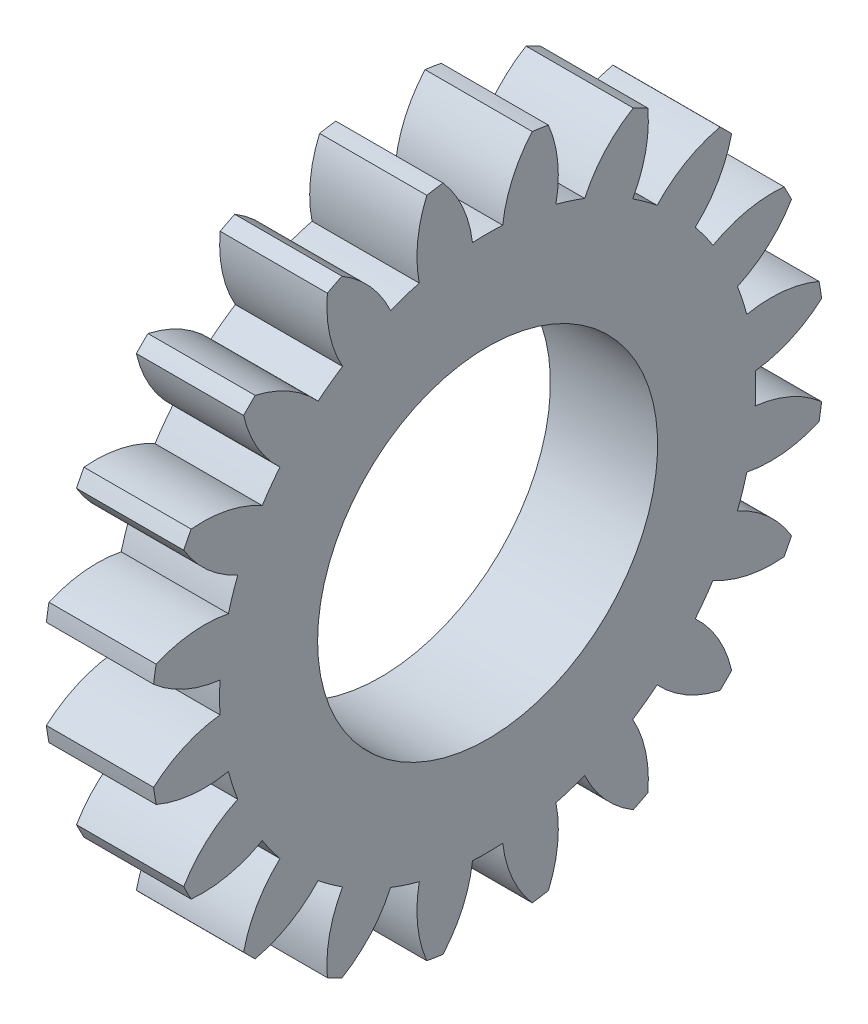
SolidWorks part; units mm, degrees
ref_plane "Plane1" through (0, 0, 0) normal (0, 0, 1) x (1, 0, 0)
ref_plane "Plane2" through (0, 0, 0) normal (0, 1, 0) x (1, 0, 0)
ref_plane "Plane3" through (0, 0, 0) normal (1, 0, 0) x (0, 0, -1)
other "Configuration Table"
sketch "HoldingSke" plane through (0, 0, 0) normal (0, 1, 0) x (1, 0, 0)
  line L0 (0, 0) -> (0.4698, -0.171)
  line L1 (-15, 0) -> (100, 0) construction
  line L2 (0, 0) -> (-2.1039, 2.3779)
  line L3 (0, 0) -> (-11.863, 4.5341)
  line L4 (0, 0) -> (8.1152, 2.9537)
  line L5 (0, 0) -> (-46.8476, -17.4728)
  line L6 (0, 0) -> (-12.4344, -8.3896)
  line L7 (-2.1039, 2.3779) -> (8.6586, 51.2059)
  line L8 (-76.2, 54.61) -> (-76.1, 54.61)
  line L9 (-71.009, 38.7566) -> (-53.1078, 45.2721)
  line L10 (-76.2, 71.12) -> (104.1128, 71.12)
  line L11 (0, 0) -> (-15, 0)
  line L12 (-76.2, 101.6) -> (-76.133, 101.6)
  line L13 (24.9733, 27.94) -> (52.9518, 28.4284)
  line L14 (24.9733, 27.94) -> (24.9743, 27.94)
  line L15 (24.9733, 27.94) -> (100.4006, 29.5858)
  line L16 (-63.627, -2) -> (-12.827, -2)
  circle A0 centre (0, 0) radius 0.5
  circle A1 centre (0, 0) radius 17.499
  circle A2 centre (0, 0) radius 37.5
  circle A3 centre (0, 0) radius 0.5
  dimension "MHD" = 34.998
  dimension "Hub_dia" = 75
  dimension "Bore" = 1
  dimension "MBD" = 1
  dimension "Num_teeth" = 20
  dimension "Pitch" = 0.5
  dimension "Overall_len" = 50
  dimension "Show_teeth" = 20
  dimension "Thickness" = 15
  dimension "OAL" = 50.0001
  dimension "T_dim" = 0.1
  dimension "Ap" = 20
  dimension "H" = 19.05
  dimension "Pitch_radius" = 180.3128
  dimension "Width" = 15
  dimension "Backlash" = 0.067
  dimension "Addendum_fac" = 1
  dimension "Dedendum_fac" = 1.25
  dimension "Clearance_fac" = 0.25
  dimension "Dedendum_add" = 0.001
  dimension "Module" = 2
sketch "BasProSke" plane through (0, 0, 0) normal (0, 1, 0) x (1, 0, 0)
  line L0 (-10, 0) -> (60, 0) construction
  line L1 (0, 0) -> (0, 22)
  line L2 (0, 0) -> (15, 0)
  line L3 (15, 0) -> (15, 22)
  line L4 (15, 22) -> (0, 22)
  dimension "Thickness" = 15
  dimension "Diameter" = 44
revolve "Base-Revolve" add sketch "BasProSke" angle 360 about L0
sketch "TooCutSke" plane through (0, 0, 0) normal (1, 0, 0) x (0, 0, -1)
  line L1 (0, 0) -> (0, 107) construction
  line L2 (0, 0) -> (-1.6864, 19.9288) construction
  line L3 (0, 0) -> (-6.2409, 39.4033) construction
  line L4 (-1.6864, 19.9288) -> (-3.1204, 19.7016) construction
  arc A0 (0.9862, 17.4712) -> (-0.9862, 17.4712) centre (0, 0) ccw
  arc A1 (2.9329, 21.8293) -> (-2.9329, 21.8293) centre (0, 0) ccw
  circle A2 centre (0, 0) radius 20 construction
  circle A3 centre (0, 0) radius 18.7939 construction
  arc A4 (-0.9862, 17.4712) -> (-2.9329, 21.8293) centre (-8.9313, 16.536) ccw
  arc A5 (2.9329, 21.8293) -> (0.9862, 17.4712) centre (8.9313, 16.536) ccw
  dimension "Root_dia" = 34.998
  dimension "Overcut_dia" = 44.0508
  dimension "Pitch_dia" = 40
  dimension "Base_dia" = 37.5877
  dimension "Flank_rad" = 8
  dimension "Half_ang" = 9
  dimension "Half_CT" = 1.4519
extrude "ToothCut" cut sketch "TooCutSke" along normal through all
fillet "Breaks" [suppressed] radius 0.04
fillet "RootFillets" [suppressed] radius 0.501
pattern_circular "TeethCuts" count 20 every 18 about axis through (-10, 0, 0) along (1, 0, 0) of "ToothCut", "RootFillets", "Breaks"
sketch "HubNeaOneSke" plane through (0, 0, 0) normal (-1, 0, 0) x (0, 0, 1)
  circle A0 centre (0, 0) radius 17.499
  dimension "Diameter" = 34.998
extrude "HubNearOne" [suppressed] add sketch "HubNeaOneSke" along normal blind 35.0001
sketch "HubNeaBotSke" plane through (0, 0, 0) normal (-1, 0, 0) x (0, 0, 1)
  circle A0 centre (0, 0) radius 17.499
  dimension "Diameter" = 34.998
extrude "HubNearBoth" [suppressed] add sketch "HubNeaBotSke" along normal blind 17.5
ref_plane "FarPln" through (15, 0, 0) normal (1, 0, 0) x (0, 0, -1)
sketch "HubFarSke" plane through (15, 0, 0) normal (1, 0, 0) x (0, 0, -1)
  circle A0 centre (0, 0) radius 17.499
  dimension "Diameter" = 34.998
extrude "HubFar" [suppressed] add sketch "HubFarSke" along normal blind 17.5
sketch "BorSke" plane through (0, 0, 0) normal (1, 0, 0) x (0, 0, -1)
  circle A0 centre (0, 0) radius 0.5
  dimension "Diameter" = 1
extrude "Bore" cut sketch "BorSke" along normal mid plane 100.0001
sketch "KeySke" plane through (0, 0, 0) normal (1, 0, 0) x (0, 0, -1)
  line L0 (-0.05, 0) -> (-0.05, 0.6)
  line L1 (-0.05, 0.6) -> (0.05, 0.6)
  line L2 (0.05, 0.6) -> (0.05, 0)
  line L3 (0, 0) -> (0, 34) construction
  line L4 (-0.05, 0) -> (0.05, 0)
  dimension "Offset" = 0.6
  dimension "Width" = 0.1
extrude "Keyway" [suppressed] cut sketch "KeySke" along normal mid plane 100.0001
pattern_circular "Keyway2" [suppressed] count 2 every 90 about axis through (-10, 0, 0) along (1, 0, 0)
sketch "Sketch1" plane through (0, 0, 0) normal (-1, 0, 0) x (0, 0, 1)
  circle A0 centre (0, 0) radius 11.1
extrude "Cut-Extrude1" cut sketch "Sketch1" against normal blind 16
sketch "Sketch2" plane through (0, 0, 0) normal (-1, 0, 0) x (0, 0, 1)
  arc A80 (17.4712, 0.9862) -> (21.8063, 2.9127) centre (16.536, 8.9313) ccw
  arc A81 (21.8063, 2.9127) -> (21.6391, 3.9684) centre (0, 0) ccw
  arc A82 (21.6391, 3.9684) -> (16.9208, 4.461) centre (18.4866, -3.3843) ccw
  arc A83 (16.9208, 4.461) -> (16.3113, 6.3368) centre (0, 0) ccw
  arc A84 (16.3113, 6.3368) -> (19.839, 9.5087) centre (12.9668, 13.6041) ccw
  arc A85 (19.839, 9.5087) -> (19.3537, 10.461) centre (0, 0) ccw
  arc A86 (19.3537, 10.461) -> (14.7141, 9.4715) centre (18.6276, 2.494) ccw
  arc A87 (14.7141, 9.4715) -> (13.5548, 11.0671) centre (0, 0) ccw
  arc A88 (13.5548, 11.0671) -> (15.9297, 15.1739) centre (8.1282, 16.9452) ccw
  arc A89 (15.9297, 15.1739) -> (15.1739, 15.9297) centre (0, 0) ccw
  arc A90 (15.1739, 15.9297) -> (11.0671, 13.5548) centre (16.9452, 8.1282) ccw
  arc A91 (11.0671, 13.5548) -> (9.4715, 14.7141) centre (0, 0) ccw
  arc A92 (9.4715, 14.7141) -> (10.461, 19.3537) centre (2.494, 18.6276) ccw
  arc A93 (10.461, 19.3537) -> (9.5087, 19.839) centre (0, 0) ccw
  arc A94 (9.5087, 19.839) -> (6.3368, 16.3113) centre (13.6041, 12.9668) ccw
  arc A95 (6.3368, 16.3113) -> (4.461, 16.9208) centre (0, 0) ccw
  arc A96 (4.461, 16.9208) -> (3.9684, 21.6391) centre (-3.3843, 18.4866) ccw
  arc A97 (3.9684, 21.6391) -> (2.9127, 21.8063) centre (0, 0) ccw
  arc A98 (2.9127, 21.8063) -> (0.9862, 17.4712) centre (8.9313, 16.536) ccw
  arc A99 (0.9862, 17.4712) -> (-0.9862, 17.4712) centre (0, 0) ccw
  arc A100 (-0.9862, 17.4712) -> (-2.9127, 21.8063) centre (-8.9313, 16.536) ccw
  arc A101 (-2.9127, 21.8063) -> (-3.9684, 21.6391) centre (0, 0) ccw
  arc A102 (-3.9684, 21.6391) -> (-4.461, 16.9208) centre (3.3843, 18.4866) ccw
  arc A103 (-4.461, 16.9208) -> (-6.3368, 16.3113) centre (0, 0) ccw
  arc A104 (-6.3368, 16.3113) -> (-9.5087, 19.839) centre (-13.6041, 12.9668) ccw
  arc A105 (-9.5087, 19.839) -> (-10.461, 19.3537) centre (0, 0) ccw
  arc A106 (-10.461, 19.3537) -> (-9.4715, 14.7141) centre (-2.494, 18.6276) ccw
  arc A107 (-9.4715, 14.7141) -> (-11.0671, 13.5548) centre (0, 0) ccw
  arc A108 (-11.0671, 13.5548) -> (-15.1739, 15.9297) centre (-16.9452, 8.1282) ccw
  arc A109 (-15.1739, 15.9297) -> (-15.9297, 15.1739) centre (0, 0) ccw
  arc A110 (-15.9297, 15.1739) -> (-13.5548, 11.0671) centre (-8.1282, 16.9452) ccw
  arc A111 (-13.5548, 11.0671) -> (-14.7141, 9.4715) centre (0, 0) ccw
  arc A112 (-14.7141, 9.4715) -> (-19.3537, 10.461) centre (-18.6276, 2.494) ccw
  arc A113 (-19.3537, 10.461) -> (-19.839, 9.5087) centre (0, 0) ccw
  arc A114 (-19.839, 9.5087) -> (-16.3113, 6.3368) centre (-12.9668, 13.6041) ccw
  arc A115 (-16.3113, 6.3368) -> (-16.9208, 4.461) centre (0, 0) ccw
  arc A116 (-16.9208, 4.461) -> (-21.6391, 3.9684) centre (-18.4866, -3.3843) ccw
  arc A117 (-21.6391, 3.9684) -> (-21.8063, 2.9127) centre (0, 0) ccw
  arc A118 (-21.8063, 2.9127) -> (-17.4712, 0.9862) centre (-16.536, 8.9313) ccw
  arc A119 (-17.4712, 0.9862) -> (-17.4712, -0.9862) centre (0, 0) ccw
  arc A120 (-17.4712, -0.9862) -> (-21.8063, -2.9127) centre (-16.536, -8.9313) ccw
  arc A121 (-21.8063, -2.9127) -> (-21.6391, -3.9684) centre (0, 0) ccw
  arc A122 (-21.6391, -3.9684) -> (-16.9208, -4.461) centre (-18.4866, 3.3843) ccw
  arc A123 (-16.9208, -4.461) -> (-16.3113, -6.3368) centre (0, 0) ccw
  arc A124 (-16.3113, -6.3368) -> (-19.839, -9.5087) centre (-12.9668, -13.6041) ccw
  arc A125 (-19.839, -9.5087) -> (-19.3537, -10.461) centre (0, 0) ccw
  arc A126 (-19.3537, -10.461) -> (-14.7141, -9.4715) centre (-18.6276, -2.494) ccw
  arc A127 (-14.7141, -9.4715) -> (-13.5548, -11.0671) centre (0, 0) ccw
  arc A128 (-13.5548, -11.0671) -> (-15.9297, -15.1739) centre (-8.1282, -16.9452) ccw
  arc A129 (-15.9297, -15.1739) -> (-15.1739, -15.9297) centre (0, 0) ccw
  arc A130 (-15.1739, -15.9297) -> (-11.0671, -13.5548) centre (-16.9452, -8.1282) ccw
  arc A131 (-11.0671, -13.5548) -> (-9.4715, -14.7141) centre (0, 0) ccw
  arc A132 (-9.4715, -14.7141) -> (-10.461, -19.3537) centre (-2.494, -18.6276) ccw
  arc A133 (-10.461, -19.3537) -> (-9.5087, -19.839) centre (0, 0) ccw
  arc A134 (-9.5087, -19.839) -> (-6.3368, -16.3113) centre (-13.6041, -12.9668) ccw
  arc A135 (-6.3368, -16.3113) -> (-4.461, -16.9208) centre (0, 0) ccw
  arc A136 (-4.461, -16.9208) -> (-3.9684, -21.6391) centre (3.3843, -18.4866) ccw
  arc A137 (-3.9684, -21.6391) -> (-2.9127, -21.8063) centre (0, 0) ccw
  arc A138 (-2.9127, -21.8063) -> (-0.9862, -17.4712) centre (-8.9313, -16.536) ccw
  arc A139 (-0.9862, -17.4712) -> (0.9862, -17.4712) centre (0, 0) ccw
  arc A140 (0.9862, -17.4712) -> (2.9127, -21.8063) centre (8.9313, -16.536) ccw
  arc A141 (2.9127, -21.8063) -> (3.9684, -21.6391) centre (0, 0) ccw
  arc A142 (3.9684, -21.6391) -> (4.461, -16.9208) centre (-3.3843, -18.4866) ccw
  arc A143 (4.461, -16.9208) -> (6.3368, -16.3113) centre (0, 0) ccw
  arc A144 (6.3368, -16.3113) -> (9.5087, -19.839) centre (13.6041, -12.9668) ccw
  arc A145 (9.5087, -19.839) -> (10.461, -19.3537) centre (0, 0) ccw
  arc A146 (10.461, -19.3537) -> (9.4715, -14.7141) centre (2.494, -18.6276) ccw
  arc A147 (9.4715, -14.7141) -> (11.0671, -13.5548) centre (0, 0) ccw
  arc A148 (11.0671, -13.5548) -> (15.1739, -15.9297) centre (16.9452, -8.1282) ccw
  arc A149 (15.1739, -15.9297) -> (15.9297, -15.1739) centre (0, 0) ccw
  arc A150 (15.9297, -15.1739) -> (13.5548, -11.0671) centre (8.1282, -16.9452) ccw
  arc A151 (13.5548, -11.0671) -> (14.7141, -9.4715) centre (0, 0) ccw
  arc A152 (14.7141, -9.4715) -> (19.3537, -10.461) centre (18.6276, -2.494) ccw
  arc A153 (19.3537, -10.461) -> (19.839, -9.5087) centre (0, 0) ccw
  arc A154 (19.839, -9.5087) -> (16.3113, -6.3368) centre (12.9668, -13.6041) ccw
  arc A155 (16.3113, -6.3368) -> (16.9208, -4.461) centre (0, 0) ccw
  arc A156 (16.9208, -4.461) -> (21.6391, -3.9684) centre (18.4866, 3.3843) ccw
  arc A157 (21.6391, -3.9684) -> (21.8063, -2.9127) centre (0, 0) ccw
  arc A158 (21.8063, -2.9127) -> (17.4712, -0.9862) centre (16.536, -8.9313) ccw
  arc A159 (17.4712, -0.9862) -> (17.4712, 0.9862) centre (0, 0) ccw
  arc A160 (17.4712, 0.9862) -> (21.8063, 2.9127) centre (16.536, 8.9313) ccw
  arc A161 (21.8063, 2.9127) -> (21.6391, 3.9684) centre (0, 0) ccw
  arc A162 (21.6391, 3.9684) -> (16.9208, 4.461) centre (18.4866, -3.3843) ccw
  arc A163 (16.9208, 4.461) -> (16.3113, 6.3368) centre (0, 0) ccw
  arc A164 (16.3113, 6.3368) -> (19.839, 9.5087) centre (12.9668, 13.6041) ccw
  arc A165 (19.839, 9.5087) -> (19.3537, 10.461) centre (0, 0) ccw
  arc A166 (19.3537, 10.461) -> (14.7141, 9.4715) centre (18.6276, 2.494) ccw
  arc A167 (14.7141, 9.4715) -> (13.5548, 11.0671) centre (0, 0) ccw
  arc A168 (13.5548, 11.0671) -> (15.9297, 15.1739) centre (8.1282, 16.9452) ccw
  arc A169 (15.9297, 15.1739) -> (15.1739, 15.9297) centre (0, 0) ccw
  arc A170 (15.1739, 15.9297) -> (11.0671, 13.5548) centre (16.9452, 8.1282) ccw
  arc A171 (11.0671, 13.5548) -> (9.4715, 14.7141) centre (0, 0) ccw
  arc A172 (9.4715, 14.7141) -> (10.461, 19.3537) centre (2.494, 18.6276) ccw
  arc A173 (10.461, 19.3537) -> (9.5087, 19.839) centre (0, 0) ccw
  arc A174 (9.5087, 19.839) -> (6.3368, 16.3113) centre (13.6041, 12.9668) ccw
  arc A175 (6.3368, 16.3113) -> (4.461, 16.9208) centre (0, 0) ccw
  arc A176 (4.461, 16.9208) -> (3.9684, 21.6391) centre (-3.3843, 18.4866) ccw
  arc A177 (3.9684, 21.6391) -> (2.9127, 21.8063) centre (0, 0) ccw
  arc A178 (2.9127, 21.8063) -> (0.9862, 17.4712) centre (8.9313, 16.536) ccw
  arc A179 (0.9862, 17.4712) -> (-0.9862, 17.4712) centre (0, 0) ccw
  arc A180 (-0.9862, 17.4712) -> (-2.9127, 21.8063) centre (-8.9313, 16.536) ccw
  arc A181 (-2.9127, 21.8063) -> (-3.9684, 21.6391) centre (0, 0) ccw
  arc A182 (-3.9684, 21.6391) -> (-4.461, 16.9208) centre (3.3843, 18.4866) ccw
  arc A183 (-4.461, 16.9208) -> (-6.3368, 16.3113) centre (0, 0) ccw
  arc A184 (-6.3368, 16.3113) -> (-9.5087, 19.839) centre (-13.6041, 12.9668) ccw
  arc A185 (-9.5087, 19.839) -> (-10.461, 19.3537) centre (0, 0) ccw
  arc A186 (-10.461, 19.3537) -> (-9.4715, 14.7141) centre (-2.494, 18.6276) ccw
  arc A187 (-9.4715, 14.7141) -> (-11.0671, 13.5548) centre (0, 0) ccw
  arc A188 (-11.0671, 13.5548) -> (-15.1739, 15.9297) centre (-16.9452, 8.1282) ccw
  arc A189 (-15.1739, 15.9297) -> (-15.9297, 15.1739) centre (0, 0) ccw
  arc A190 (-15.9297, 15.1739) -> (-13.5548, 11.0671) centre (-8.1282, 16.9452) ccw
  arc A191 (-13.5548, 11.0671) -> (-14.7141, 9.4715) centre (0, 0) ccw
  arc A192 (-14.7141, 9.4715) -> (-19.3537, 10.461) centre (-18.6276, 2.494) ccw
  arc A193 (-19.3537, 10.461) -> (-19.839, 9.5087) centre (0, 0) ccw
  arc A194 (-19.839, 9.5087) -> (-16.3113, 6.3368) centre (-12.9668, 13.6041) ccw
  arc A195 (-16.3113, 6.3368) -> (-16.9208, 4.461) centre (0, 0) ccw
  arc A196 (-16.9208, 4.461) -> (-21.6391, 3.9684) centre (-18.4866, -3.3843) ccw
  arc A197 (-21.6391, 3.9684) -> (-21.8063, 2.9127) centre (0, 0) ccw
  arc A198 (-21.8063, 2.9127) -> (-17.4712, 0.9862) centre (-16.536, 8.9313) ccw
  arc A199 (-17.4712, 0.9862) -> (-17.4712, -0.9862) centre (0, 0) ccw
  arc A200 (-17.4712, -0.9862) -> (-21.8063, -2.9127) centre (-16.536, -8.9313) ccw
  arc A201 (-21.8063, -2.9127) -> (-21.6391, -3.9684) centre (0, 0) ccw
  arc A202 (-21.6391, -3.9684) -> (-16.9208, -4.461) centre (-18.4866, 3.3843) ccw
  arc A203 (-16.9208, -4.461) -> (-16.3113, -6.3368) centre (0, 0) ccw
  arc A204 (-16.3113, -6.3368) -> (-19.839, -9.5087) centre (-12.9668, -13.6041) ccw
  arc A205 (-19.839, -9.5087) -> (-19.3537, -10.461) centre (0, 0) ccw
  arc A206 (-19.3537, -10.461) -> (-14.7141, -9.4715) centre (-18.6276, -2.494) ccw
  arc A207 (-14.7141, -9.4715) -> (-13.5548, -11.0671) centre (0, 0) ccw
  arc A208 (-13.5548, -11.0671) -> (-15.9297, -15.1739) centre (-8.1282, -16.9452) ccw
  arc A209 (-15.9297, -15.1739) -> (-15.1739, -15.9297) centre (0, 0) ccw
  arc A210 (-15.1739, -15.9297) -> (-11.0671, -13.5548) centre (-16.9452, -8.1282) ccw
  arc A211 (-11.0671, -13.5548) -> (-9.4715, -14.7141) centre (0, 0) ccw
  arc A212 (-9.4715, -14.7141) -> (-10.461, -19.3537) centre (-2.494, -18.6276) ccw
  arc A213 (-10.461, -19.3537) -> (-9.5087, -19.839) centre (0, 0) ccw
  arc A214 (-9.5087, -19.839) -> (-6.3368, -16.3113) centre (-13.6041, -12.9668) ccw
  arc A215 (-6.3368, -16.3113) -> (-4.461, -16.9208) centre (0, 0) ccw
  arc A216 (-4.461, -16.9208) -> (-3.9684, -21.6391) centre (3.3843, -18.4866) ccw
  arc A217 (-3.9684, -21.6391) -> (-2.9127, -21.8063) centre (0, 0) ccw
  arc A218 (-2.9127, -21.8063) -> (-0.9862, -17.4712) centre (-8.9313, -16.536) ccw
  arc A219 (-0.9862, -17.4712) -> (0.9862, -17.4712) centre (0, 0) ccw
  arc A220 (0.9862, -17.4712) -> (2.9127, -21.8063) centre (8.9313, -16.536) ccw
  arc A221 (2.9127, -21.8063) -> (3.9684, -21.6391) centre (0, 0) ccw
  arc A222 (3.9684, -21.6391) -> (4.461, -16.9208) centre (-3.3843, -18.4866) ccw
  arc A223 (4.461, -16.9208) -> (6.3368, -16.3113) centre (0, 0) ccw
  arc A224 (6.3368, -16.3113) -> (9.5087, -19.839) centre (13.6041, -12.9668) ccw
  arc A225 (9.5087, -19.839) -> (10.461, -19.3537) centre (0, 0) ccw
  arc A226 (10.461, -19.3537) -> (9.4715, -14.7141) centre (2.494, -18.6276) ccw
  arc A227 (9.4715, -14.7141) -> (11.0671, -13.5548) centre (0, 0) ccw
  arc A228 (11.0671, -13.5548) -> (15.1739, -15.9297) centre (16.9452, -8.1282) ccw
  arc A229 (15.1739, -15.9297) -> (15.9297, -15.1739) centre (0, 0) ccw
  arc A230 (15.9297, -15.1739) -> (13.5548, -11.0671) centre (8.1282, -16.9452) ccw
  arc A231 (13.5548, -11.0671) -> (14.7141, -9.4715) centre (0, 0) ccw
  arc A232 (14.7141, -9.4715) -> (19.3537, -10.461) centre (18.6276, -2.494) ccw
  arc A233 (19.3537, -10.461) -> (19.839, -9.5087) centre (0, 0) ccw
  arc A234 (19.839, -9.5087) -> (16.3113, -6.3368) centre (12.9668, -13.6041) ccw
  arc A235 (16.3113, -6.3368) -> (16.9208, -4.461) centre (0, 0) ccw
  arc A236 (16.9208, -4.461) -> (21.6391, -3.9684) centre (18.4866, 3.3843) ccw
  arc A237 (21.6391, -3.9684) -> (21.8063, -2.9127) centre (0, 0) ccw
  arc A238 (21.8063, -2.9127) -> (17.4712, -0.9862) centre (16.536, -8.9313) ccw
  arc A239 (17.4712, -0.9862) -> (17.4712, 0.9862) centre (0, 0) ccw
  dimension "D1" = 0
extrude "Cut-Extrude2" cut sketch "Sketch2" against normal blind 8
equation "' \"Module@HoldingSke\" = 6.35"
equation "' \"Num_teeth@HoldingSke\" = 12"
equation "' \"Ap@HoldingSke\" =  20"
equation "' \"Ap@HoldingSke\" = 20"
equation "' \"Width@HoldingSke\" = 0.5 * 25.4"
equation "' \"Hub_dia@HoldingSke\"= 1 * 25.4"
equation "' \"Hub_dia@HoldingSke\" = 1 * 25.4"
equation "' \"Overall_len@HoldingSke\" = 1.0 * 25.4"
equation "' \"Bore@HoldingSke\" = 0.75 * 25.4"
equation "' \"T_dim@HoldingSke\" = 0.1 * 25.4"
equation "' \"Width@KeySke\" = 0.25 * 25.4"
equation "' \"Show_teeth@HoldingSke\" = 13"
equation "' \"Backlash@HoldingSke\" = 0.009 * 25.4"
equation "' \"Addendum_fac@HoldingSke\" = 1.0"
equation "' \"Dedendum_fac@HoldingSke\" = 1.25"
equation "' \"Dedendum_add@HoldingSke\" = 0.00005 * 25.4"
equation "' \"Clearance_fac@HoldingSke\" = 0.25"
equation "\"Pitch@HoldingSke\" = 1 / \"Module@HoldingSke\""
equation "\"Overcut_dia@TooCutSke\" = (\"Num_teeth@HoldingSke\" + 2 * \"Addendum_fac@HoldingSke\") / \"Pitch@HoldingSke\" + 0.002 * 25.4"
equation "\"Pitch_dia@TooCutSke\" = \"Num_teeth@HoldingSke\" / \"Pitch@HoldingSke\""
equation "\"Base_dia@TooCutSke\" = \"Num_teeth@HoldingSke\" / \"Pitch@HoldingSke\" * cos((\"Ap@HoldingSke\"  * 3.14159265 / 180))"
equation "\"Root_dia@TooCutSke\" = (\"Num_teeth@HoldingSke\" + 2) / \"Pitch@HoldingSke\" - 2 * (\"Addendum_fac@HoldingSke\" + \"Dedendum_fac@HoldingSke\") / \"Pitch@HoldingSke\" - \"Dedendum_add@HoldingSke\" * 2"
equation "\"Half_ang@TooCutSke\" = 180 / \"Num_teeth@HoldingSke\""
equation "\"Half_CT@TooCutSke\" = \"Num_teeth@HoldingSke\" / \"Pitch@HoldingSke\" * sin((3.14159265 / 2 / \"Num_teeth@HoldingSke\")) / 2 - 7 * \"Backlash@HoldingSke\" / 4"
equation "\"Flank_rad@TooCutSke\" = \"Num_teeth@HoldingSke\" / \"Pitch@HoldingSke\" / 5"
equation "\"Radius@RootFillets\" = \"Clearance_fac@HoldingSke\" / \"Pitch@HoldingSke\" + \"Dedendum_add@HoldingSke\""
equation "\"Break_rad@Breaks\" = 0.02 / \"Pitch@HoldingSke\""
equation "\"Thickness@HoldingSke\" = \"Width@HoldingSke\""
equation "\"OAL@HoldingSke\" = \"Thickness@HoldingSke\""
equation "\"MHD@HoldingSke\" = (\"Num_teeth@HoldingSke\" + 2) / \"Pitch@HoldingSke\" - 2 * (\"Addendum_fac@HoldingSke\" + \"Dedendum_fac@HoldingSke\")  / \"Pitch@HoldingSke\" - \"Dedendum_add@HoldingSke\" * 2"
equation "\"MBD@HoldingSke\" = (\"Num_teeth@HoldingSke\" + 2) / \"Pitch@HoldingSke\" - 2 * (\"Addendum_fac@HoldingSke\" + \"Dedendum_fac@HoldingSke\")  / \"Pitch@HoldingSke\" - \"Dedendum_add@HoldingSke\" * 2 - 0.002 * 25.4"
equation "\"MHD@HoldingSke\" = ((sgn( \"MHD@HoldingSke\" - \"Hub_dia@HoldingSke\" )-1)*( \"MHD@HoldingSke\" - \"Hub_dia@HoldingSke\" ))/-2+ \"Hub_dia@HoldingSke\""
equation "\"MBD@HoldingSke\" = ((sgn( \"MBD@HoldingSke\" - \"Bore@HoldingSke\" )-1)*( \"MBD@HoldingSke\" - \"Bore@HoldingSke\" ))/-2+ \"Bore@HoldingSke\""
equation "\"OAL@HoldingSke\" = ((sgn( \"OAL@HoldingSke\" - \"Overall_len@HoldingSke\" )+1)*( \"OAL@HoldingSke\" - \"Overall_len@HoldingSke\" ))/2 + \"Overall_len@HoldingSke\" + 0.000002 * 25.4"
equation "\"Num_teeth@TeethCuts\" = int( \"Show_teeth@HoldingSke\" ) + 1"
equation "\"Num_teeth@TeethCuts\" = ((sgn( \"Num_teeth@TeethCuts\" - \"Num_teeth@HoldingSke\" )-1)*( \"Num_teeth@TeethCuts\" - \"Num_teeth@HoldingSke\" ))/-2+ \"Num_teeth@HoldingSke\""
equation "\"Num_teeth@TeethCuts\" = ((sgn( \"Num_teeth@TeethCuts\" - 2.0)+1)*( \"Num_teeth@TeethCuts\" - 2.0))/2 +2.0"
equation "\"Angle@TeethCuts\" = 360.0 / \"Num_teeth@HoldingSke\""
equation "\"Diameter@BasProSke\" = (\"Num_teeth@HoldingSke\" + 2 * \"Addendum_fac@HoldingSke\") / \"Pitch@HoldingSke\""
equation "\"Thickness@BasProSke\"  = \"Thickness@HoldingSke\""
equation "' \"Fillet_rad@BasProSke\" =  \"Thickness@HoldingSke\" * 0.05"
equation "' \"Fillet_rad@BasProSke\" = \"Thickness@HoldingSke\" * 0.05"
equation "\"MHD@HoldingSke\" = ((sgn( \"MHD@HoldingSke\" - \"Root_dia@TooCutSke\" )-1)*( \"MHD@HoldingSke\" - \"Root_dia@TooCutSke\" ))/-2+ \"Root_dia@TooCutSke\""
equation "\"Diameter@HubNeaOneSke\" = \"MHD@HoldingSke\""
equation "\"Length@HubNearOne\" = \"OAL@HoldingSke\" - \"Thickness@BasProSke\""
equation "\"Diameter@HubNeaBotSke\" = \"MHD@HoldingSke\""
equation "\"Length@HubNearBoth\" = ( \"OAL@HoldingSke\" - \"Thickness@BasProSke\" ) / 2.0"
equation "\"Thickness@FarPln\" = \"Thickness@BasProSke\""
equation "\"Diameter@HubFarSke\" = \"MHD@HoldingSke\""
equation "\"Length@HubFar\" = ( \"OAL@HoldingSke\" - \"Thickness@BasProSke\" ) / 2.0"
equation "\"Diameter@BorSke\" = \"MBD@HoldingSke\""
equation "\"D1@Bore\" = \"OAL@HoldingSke\" * 2.0"
equation "\"D1@Keyway\" = \"OAL@HoldingSke\" * 2.0"
equation "\"Offset@KeySke\" = \"T_dim@HoldingSke\" + \"MBD@HoldingSke\" / 2.0"
